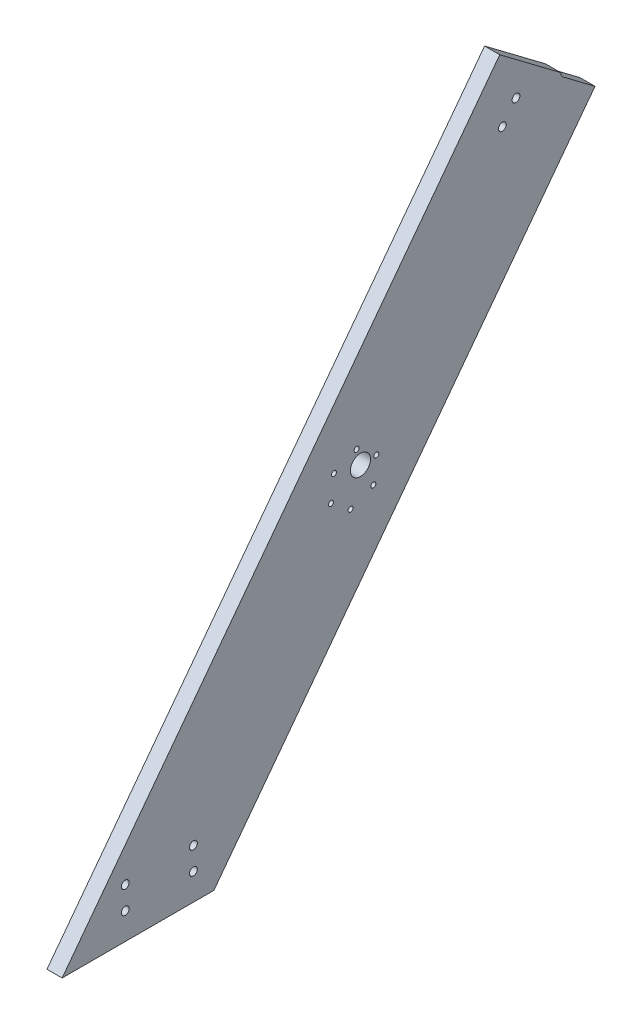
SolidWorks part; units mm, degrees
material "PC High Viscosity"
ref_plane "Front Plane" through (0, 0, 0) normal (0, 0, 1) x (1, 0, 0)
ref_plane "Top Plane" through (0, 0, 0) normal (0, 1, 0) x (1, 0, 0)
ref_plane "Right Plane" through (0, 0, 0) normal (1, 0, 0) x (0, 0, -1)
sketch "Sketch1" plane through (0, 0, 0) normal (1, 0, 0) x (0, 0, -1)
  line L0 (0, 0) -> (275.1498, 365.1362)
  line L2 (336.0059, 319.2779) -> (95.4127, 0)
  line L3 (95.4127, 0) -> (0, 0)
  line L4 (275.1498, 365.1362) -> (336.0059, 319.2779)
  dimension "D1" = 53
  dimension "D2" = 457.2
  dimension "D3" = 76.2
  dimension "D4" = 90
extrude "Boss-Extrude1" add sketch "Sketch1" along normal blind 9.525
sketch "Sketch2" plane through (9.525, 0, 0) normal (1, 0, 0) x (0, 0, -1)
  line L0 (335.0505, 318.01) -> (314.7651, 333.2961)
  line L1 (95.4127, 0) -> (336.0059, 319.2779) construction
  line L2 (336.0059, 319.2779) -> (313.5246, 336.2187)
  line L3 (336.0059, 319.2779) -> (335.0505, 318.01)
  line L4 (336.0059, 319.2779) -> (275.1498, 365.1362) construction
  arc A0 (313.5246, 336.2187) -> (314.7651, 333.2961) centre (316.6759, 335.8318) ccw
  dimension "D1" = 25.4
  dimension "D3" = 3.175
  dimension "D2" = 1.5875
extrude "Cut-Extrude1" cut sketch "Sketch2" against normal through all
sketch "Sketch3" plane through (9.525, 0, 0) normal (1, 0, 0) x (0, 0, -1)
  line L0 (187.5691, 185.6042) -> (183.289, 179.9243) construction
  line L1 (275.1498, 365.1362) -> (0, 0) construction
  line L2 (95.4127, 0) -> (335.0505, 318.01) construction
  line L3 (313.5246, 336.2187) -> (275.1498, 365.1362) construction
  line L4 (183.289, 179.9243) -> (195.6631, 170.5997) construction
  circle A0 centre (187.5691, 185.6042) radius 6.35
  circle A1 centre (183.289, 179.9243) radius 15.494 construction
  circle A2 centre (195.6631, 170.5997) radius 1.5875
  circle A3 centre (181.4008, 164.5458) radius 1.5875
  circle A4 centre (169.0267, 173.8703) radius 1.5875
  circle A5 centre (170.915, 189.2488) radius 1.5875
  circle A6 centre (185.1773, 195.3028) radius 1.5875
  circle A7 centre (197.5513, 185.9783) radius 1.5875
  point P25 (183.289, 179.9243)
  dimension "D1" = 38.1
  dimension "D4" = 12.7
  dimension "D5" = 30.988
  dimension "D6" = 3.175
  dimension "D2" = 203.2
  dimension "D3" = 7.112
  dimension "D7" = 6
extrude "Cut-Extrude2" cut sketch "Sketch3" against normal through all
sketch "Sketch4" plane through (9.525, 0, 0) normal (1, 0, 0) x (0, 0, -1)
  line L0 (285.3463, 336.4617) -> (276.7861, 325.1019) construction
  line L1 (275.1498, 365.1362) -> (0, 0) construction
  line L2 (313.5246, 336.2187) -> (275.1498, 365.1362) construction
  line L3 (0, 0) -> (95.4127, 0) construction
  line L4 (27.6225, 0) -> (27.6225, 39.878) construction
  line L5 (27.6225, 0) -> (51.7525, 0) construction
  line L6 (27.6225, 39.878) -> (51.7525, 39.878)
  line L7 (51.7525, 0) -> (51.7525, 39.878) construction
  line L8 (70.485, 0) -> (70.485, 39.878) construction
  line L9 (70.485, 0) -> (94.615, 0) construction
  line L10 (70.485, 39.878) -> (94.615, 39.878) construction
  line L11 (94.615, 0) -> (94.615, 39.878) construction
  circle A0 centre (285.3463, 336.4617) radius 2.4638
  circle A1 centre (276.7861, 325.1019) radius 2.4638
  circle A2 centre (39.6875, 30.988) radius 2.4638
  circle A3 centre (39.6875, 16.764) radius 2.4638
  circle A4 centre (82.55, 30.988) radius 2.4638
  circle A5 centre (82.55, 16.764) radius 2.4638
  point P22 (281.0662, 330.7818)
  dimension "D1" = 4.9276
  dimension "D2" = 16.764
  dimension "D3" = 14.224
  dimension "D4" = 14.224
  dimension "D5" = 16.764
  dimension "D6" = 25.4
  dimension "D7" = 24.13
  dimension "D8" = 39.878
  dimension "D9" = 12.065
  dimension "D10" = 12.065
  dimension "D11" = 39.6875
  dimension "D12" = 82.55
extrude "Cut-Extrude3" cut sketch "Sketch4" against normal through all contours A3 | A2 | A4 | A5 | A0 | A1
